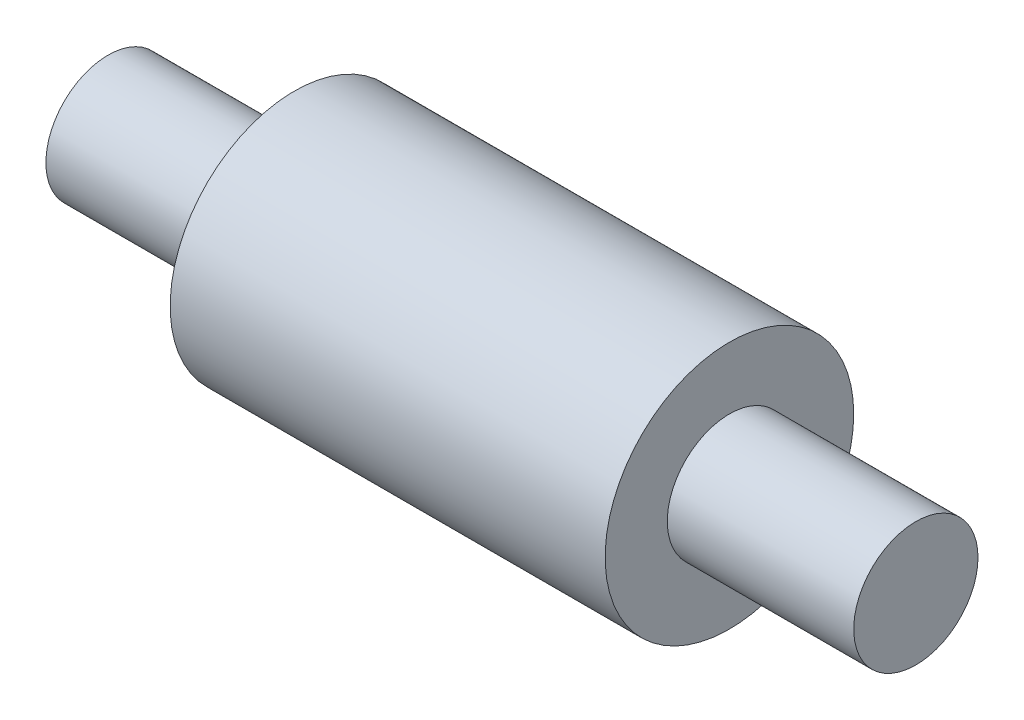
SolidWorks part; units mm, degrees
material "1023 Carbon Steel Sheet (SS)"
ref_plane "Front Plane" through (0, 0, 0) normal (0, 0, 1) x (1, 0, 0)
ref_plane "Top Plane" through (0, 0, 0) normal (0, 1, 0) x (1, 0, 0)
ref_plane "Right Plane" through (0, 0, 0) normal (1, 0, 0) x (0, 0, -1)
sketch "Sketch3" plane through (0, 0, 0) normal (0, 1, 0) x (1, 0, 0)
  line L0 (0, 0) -> (-65.3612, 0) construction
  line L1 (-56.0166, 0) -> (-56.0166, 10)
  line L2 (-56.0166, 10) -> (-26.0166, 10)
  line L3 (43.9834, 10) -> (43.9834, 20)
  line L4 (43.9834, 20) -> (-26.0166, 20)
  line L5 (-26.0166, 20) -> (-26.0166, 10)
  line L6 (43.9834, 10) -> (73.9834, 10)
  line L7 (73.9834, 10) -> (73.9834, 0)
  line L8 (73.9834, 0) -> (-56.0166, 0)
  dimension "D1" = 10
  dimension "D2" = 43.9834
  dimension "D3" = 73.9834
  dimension "D4" = 26.0166
revolve "Revolve1" add sketch "Sketch3" angle 360 about L0
